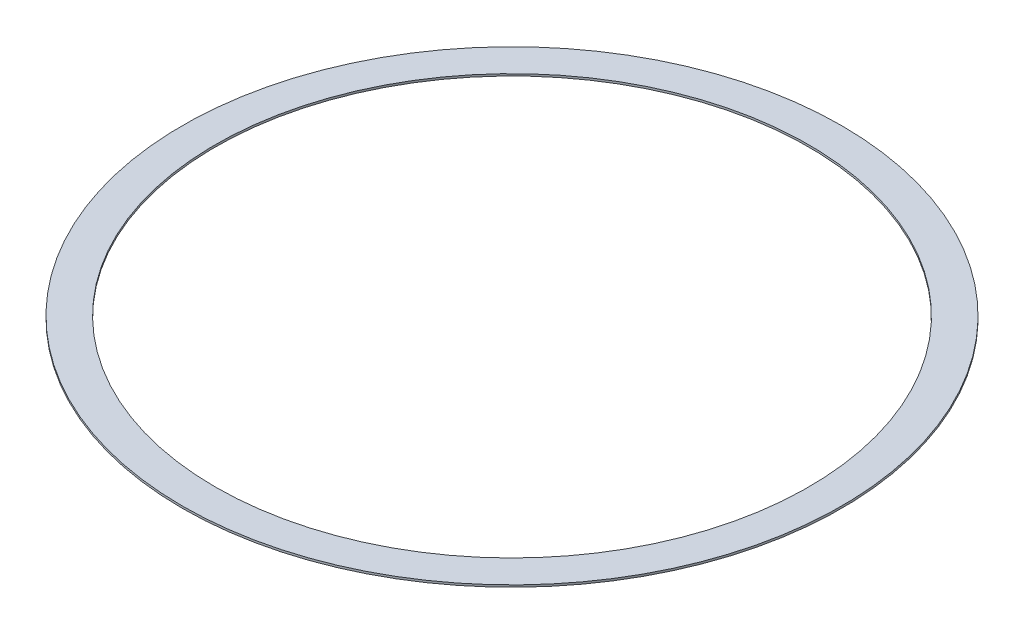
SolidWorks part; units mm, degrees
ref_plane "Front Plane" through (0, 0, 0) normal (0, 0, 1) x (1, 0, 0)
ref_plane "Top Plane" through (0, 0, 0) normal (0, 1, 0) x (1, 0, 0)
ref_plane "Right Plane" through (0, 0, 0) normal (1, 0, 0) x (0, 0, -1)
sketch "Sketch1" plane through (0, 0, 0) normal (0, 1, 0) x (1, 0, 0)
  circle A0 centre (0, 0) radius 228.6
  circle A1 centre (0, 0) radius 254
  dimension "D1" = 457.2
  dimension "D2" = 508
extrude "Boss-Extrude1" add sketch "Sketch1" along normal blind 1.5875
